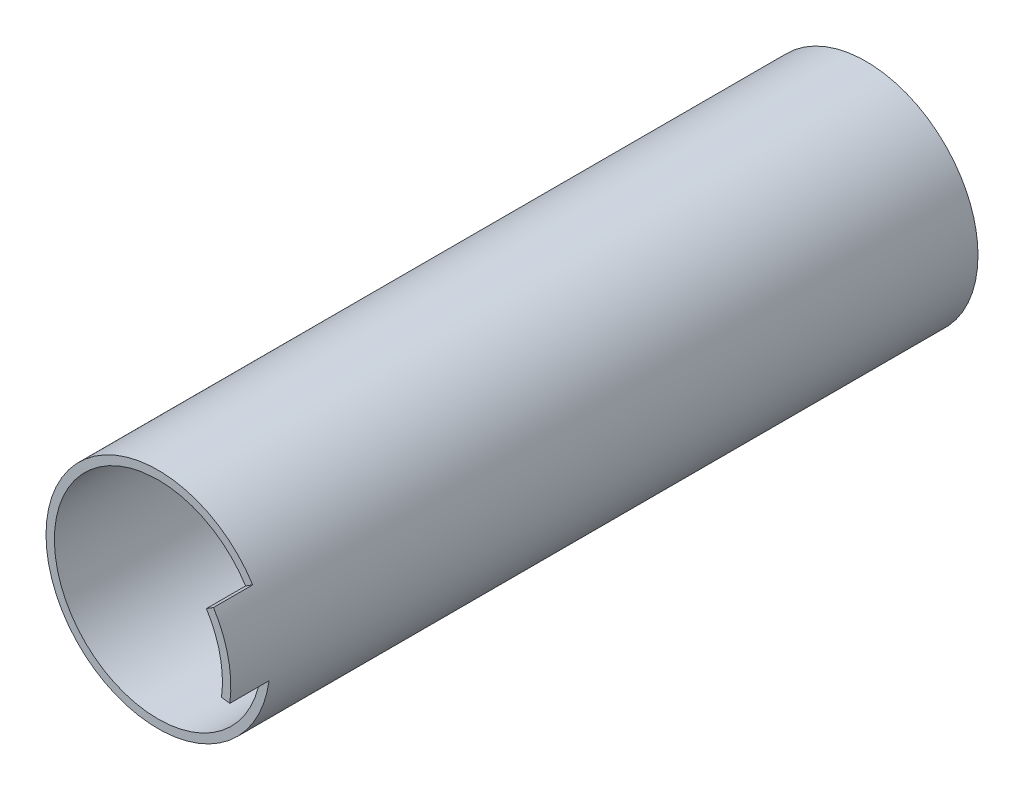
SolidWorks part; units mm, degrees
ref_plane "Спереди" through (0, 0, 0) normal (0, 0, 1) x (1, 0, 0)
ref_plane "Сверху" through (0, 0, 0) normal (0, 1, 0) x (1, 0, 0)
ref_plane "Справа" through (0, 0, 0) normal (1, 0, 0) x (0, 0, -1)
sketch "Эскиз2" plane through (0, 0, 0) normal (0, 0, 1) x (1, 0, 0)
  circle A0 centre (0, 0) radius 20
  circle A1 centre (0, 0) radius 18.5
  dimension "D1" = 40
  dimension "D2" = 37
extrude "Бобышка-Вытянуть1" add sketch "Эскиз2" along normal blind 126.4
sketch "Эскиз5" plane through (0, 0, 0) normal (0, 0, -1) x (-1, 0, 0)
  line L0 (0, 0) -> (0, 18.5) construction
  line L1 (0, 0) -> (2.9901, 18.2568) construction
  line L2 (0, 18.5) -> (0, 9.2195)
  line L3 (2.9901, 18.2568) -> (1.4901, 9.0983)
  circle A0 centre (0, 0) radius 18.5 construction
  arc A1 (0, 18.5) -> (2.9901, 18.2568) centre (0, 0) cw
  arc A2 (1.4901, 9.0983) -> (3.3687, 3.6948) centre (7.4112, 8.1286) ccw
  circle A3 centre (0, 0) radius 3
  arc A4 (-2.7273, 4.1907) -> (3.3687, 3.6948) centre (0, 0) ccw
  arc A5 (0, 9.2195) -> (-2.7273, 4.1907) centre (-6, 9.2195) cw
  point P16 (0, 5)
  dimension "D2" = 5
  dimension "D3" = 6
  dimension "D4" = 6
  dimension "D1" = 3
extrude "Бобышка-Вытянуть3" add sketch "Эскиз5" against normal through all
sketch "Sketch1" plane through (0, 0, 0) normal (0, 0, -1) x (-1, 0, 0)
  line L0 (0, 18.5) -> (2.9901, 18.2568)
  arc A2 (0, 18.5) -> (2.9901, 18.2568) centre (0, 0) ccw
  dimension "D1" = 18.5
extrude "Cut-Extrude1" cut sketch "Sketch1" against normal blind 59
sketch "Sketch2" plane through (0, 0, 126.4) normal (0, 0, 1) x (1, 0, 0)
  line L0 (0, 18.5) -> (-2.9901, 18.2568)
  arc A2 (0, 18.5) -> (-2.9901, 18.2568) centre (0, 0) cw
  dimension "D1" = 18.5
extrude "Cut-Extrude2" cut sketch "Sketch2" against normal blind 59
sketch "Sketch3" plane through (0, 0, 0) normal (0, 0, 1) x (1, 0, 0)
  line L0 (5, 0) -> (5, 16.7705)
  line L1 (-5, 0) -> (-5, 16.7705)
  circle A0 centre (0, 0) radius 5 construction
  circle A1 centre (0, 0) radius 3
  arc A2 (5, 0) -> (-5, 0) centre (0, 0) cw
  arc A3 (5, 16.7705) -> (-5, 16.7705) centre (0, 0) ccw
  arc A4 (-2.9901, 18.2568) -> (0, 18.5) centre (0, 0) ccw construction
  dimension "D1" = 10
  dimension "D2" = 6
  dimension "D3" = 1
sketch "Sketch6" plane through (0, 0, 126.4) normal (0, 0, 1) x (1, 0, 0)
  line L0 (20, 0) -> (0, 0) construction
  line L2 (0, 0) -> (19.8206, -2.6728) construction
  line L3 (0, 0) -> (16.9015, 10.6929) construction
  line L4 (16.9015, 10.6929) -> (15.6339, 9.891)
  line L5 (19.8206, -2.6728) -> (18.3341, -2.4723)
  circle A1 centre (0, 0) radius 20 construction
  arc A3 (16.9015, 10.6929) -> (19.8206, -2.6728) centre (0, 0) cw
  arc A5 (15.6339, 9.891) -> (18.3341, -2.4723) centre (0, 0) cw
  arc A6 (-2.9901, 18.2568) -> (0, 18.5) centre (0, 0) ccw construction
  dimension "D1" = 40
  dimension "D2" = 7.68
extrude "Boss-Extrude4" add sketch "Sketch6" along normal blind 7
extrude "Boss-Extrude6" add sketch "Sketch3" along normal offset from surface (58.6 mm away) 0.4 separate body up to face at (-0.7247, 8.9083, 59)
